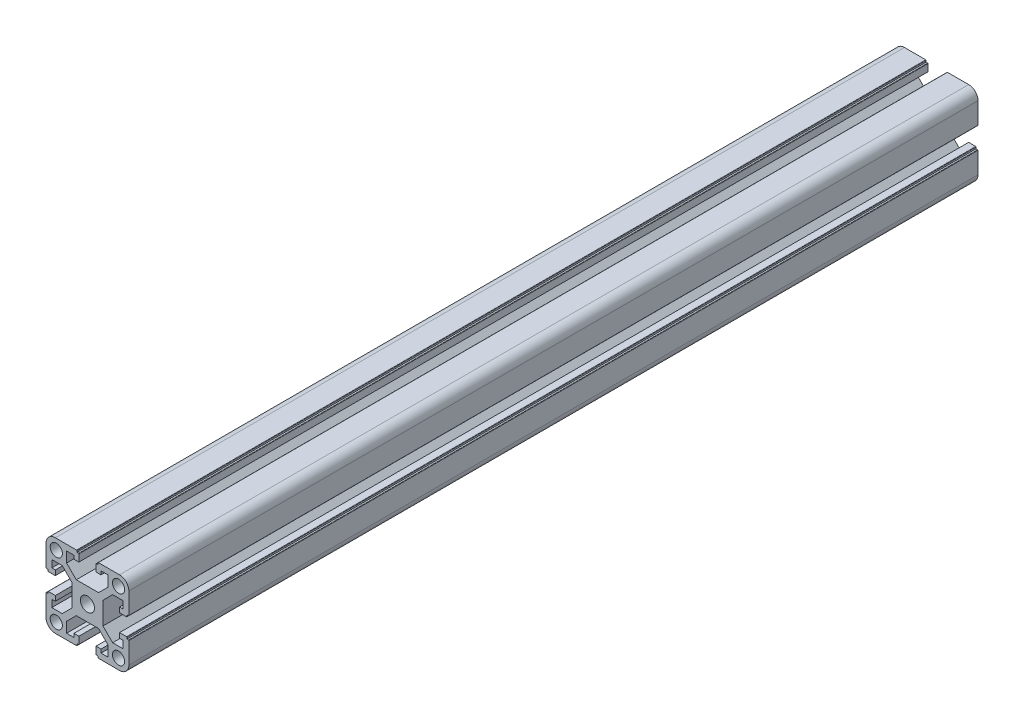
SolidWorks part; units mm, degrees
material "6061-T6 (SS)"
ref_plane "前视基准面" through (0, 0, 0) normal (0, 0, 1) x (1, 0, 0)
ref_plane "上视基准面" through (0, 0, 0) normal (0, 1, 0) x (1, 0, 0)
ref_plane "右视基准面" through (0, 0, 0) normal (1, 0, 0) x (0, 0, -1)
ref_plane "基准面1" through (0, 0, 50) normal (0, 0, 1) x (1, 0, 0)
sketch "草图1" plane through (0, 0, 50) normal (0, 0, 1) x (1, 0, 0)
  line L0 (-1518.245, 3588.0043) -> (-1518.245, 3582.9756)
  line L1 (-1518.245, 3582.9756) -> (-1522.9163, 3578.3043)
  line L2 (-1522.9163, 3578.3043) -> (-1533.6737, 3578.3043)
  line L3 (-1533.6737, 3578.3043) -> (-1538.345, 3582.9756)
  line L4 (-1538.345, 3582.9756) -> (-1538.345, 3588.0043)
  line L5 (-1538.345, 3588.0043) -> (-1534.845, 3588.0043)
  line L6 (-1534.845, 3588.0043) -> (-1534.845, 3586.3043)
  line L7 (-1534.845, 3586.3043) -> (-1532.445, 3586.3043)
  line L8 (-1532.445, 3586.3043) -> (-1532.445, 3589.7043)
  line L9 (-1532.645, 3589.9043) -> (-1533.345, 3589.9043)
  line L10 (-1533.345, 3589.9043) -> (-1533.345, 3590.6043)
  line L11 (-1533.545, 3590.8043) -> (-1543.795, 3590.8043)
  line L12 (-1548.295, 3586.3043) -> (-1548.295, 3576.0543)
  line L13 (-1548.095, 3575.8543) -> (-1547.395, 3575.8543)
  line L14 (-1547.395, 3575.8543) -> (-1547.395, 3575.1543)
  line L15 (-1547.195, 3574.9543) -> (-1543.795, 3574.9543)
  line L16 (-1543.795, 3574.9543) -> (-1543.795, 3577.3543)
  line L17 (-1543.795, 3577.3543) -> (-1545.495, 3577.3543)
  line L18 (-1545.495, 3577.3543) -> (-1545.495, 3580.8543)
  line L19 (-1545.495, 3580.8543) -> (-1540.4663, 3580.8543)
  line L20 (-1540.4663, 3580.8543) -> (-1535.795, 3576.183)
  line L21 (-1535.795, 3576.183) -> (-1535.795, 3565.4256)
  line L22 (-1535.795, 3565.4256) -> (-1540.4663, 3560.7543)
  line L23 (-1540.4663, 3560.7543) -> (-1545.495, 3560.7543)
  line L24 (-1545.495, 3560.7543) -> (-1545.495, 3564.2543)
  line L25 (-1545.495, 3564.2543) -> (-1543.795, 3564.2543)
  line L26 (-1543.795, 3564.2543) -> (-1543.795, 3566.6543)
  line L27 (-1543.795, 3566.6543) -> (-1547.195, 3566.6543)
  line L28 (-1547.395, 3566.4543) -> (-1547.395, 3565.7543)
  line L29 (-1547.395, 3565.7543) -> (-1548.095, 3565.7543)
  line L30 (-1548.295, 3565.5543) -> (-1548.295, 3555.3043)
  line L31 (-1543.795, 3550.8043) -> (-1533.545, 3550.8043)
  line L32 (-1533.345, 3551.0043) -> (-1533.345, 3551.7043)
  line L33 (-1533.345, 3551.7043) -> (-1532.645, 3551.7043)
  line L34 (-1532.445, 3551.9043) -> (-1532.445, 3555.3043)
  line L35 (-1532.445, 3555.3043) -> (-1534.845, 3555.3043)
  line L36 (-1534.845, 3555.3043) -> (-1534.845, 3553.6043)
  line L37 (-1534.845, 3553.6043) -> (-1538.345, 3553.6043)
  line L38 (-1538.345, 3553.6043) -> (-1538.345, 3558.633)
  line L39 (-1538.345, 3558.633) -> (-1533.6737, 3563.3043)
  line L40 (-1533.6737, 3563.3043) -> (-1522.9163, 3563.3043)
  line L41 (-1522.9163, 3563.3043) -> (-1518.245, 3558.633)
  line L42 (-1518.245, 3558.633) -> (-1518.245, 3553.6043)
  line L43 (-1518.245, 3553.6043) -> (-1521.745, 3553.6043)
  line L44 (-1521.745, 3553.6043) -> (-1521.745, 3555.3043)
  line L45 (-1521.745, 3555.3043) -> (-1524.145, 3555.3043)
  line L46 (-1524.145, 3555.3043) -> (-1524.145, 3551.9043)
  line L47 (-1523.945, 3551.7043) -> (-1523.245, 3551.7043)
  line L48 (-1523.245, 3551.7043) -> (-1523.245, 3551.0043)
  line L49 (-1523.045, 3550.8043) -> (-1512.795, 3550.8043)
  line L50 (-1508.295, 3555.3043) -> (-1508.295, 3565.5543)
  line L51 (-1508.495, 3565.7543) -> (-1509.195, 3565.7543)
  line L52 (-1509.195, 3565.7543) -> (-1509.195, 3566.4543)
  line L53 (-1509.395, 3566.6543) -> (-1512.795, 3566.6543)
  line L54 (-1512.795, 3566.6543) -> (-1512.795, 3564.2543)
  line L55 (-1512.795, 3564.2543) -> (-1511.095, 3564.2543)
  line L56 (-1511.095, 3564.2543) -> (-1511.095, 3560.7543)
  line L57 (-1511.095, 3560.7543) -> (-1516.1237, 3560.7543)
  line L58 (-1516.1237, 3560.7543) -> (-1520.795, 3565.4256)
  line L59 (-1520.795, 3565.4256) -> (-1520.795, 3576.183)
  line L60 (-1520.795, 3576.183) -> (-1516.1237, 3580.8543)
  line L61 (-1516.1237, 3580.8543) -> (-1511.095, 3580.8543)
  line L62 (-1511.095, 3580.8543) -> (-1511.095, 3577.3543)
  line L63 (-1511.095, 3577.3543) -> (-1512.795, 3577.3543)
  line L64 (-1512.795, 3577.3543) -> (-1512.795, 3574.9543)
  line L65 (-1512.795, 3574.9543) -> (-1509.395, 3574.9543)
  line L66 (-1509.195, 3575.1543) -> (-1509.195, 3575.8543)
  line L67 (-1509.195, 3575.8543) -> (-1508.495, 3575.8543)
  line L68 (-1508.295, 3576.0543) -> (-1508.295, 3586.3043)
  line L69 (-1512.795, 3590.8043) -> (-1523.045, 3590.8043)
  line L70 (-1523.245, 3590.6043) -> (-1523.245, 3589.9043)
  line L71 (-1523.245, 3589.9043) -> (-1523.945, 3589.9043)
  line L72 (-1524.145, 3589.7043) -> (-1524.145, 3586.3043)
  line L73 (-1524.145, 3586.3043) -> (-1521.745, 3586.3043)
  line L74 (-1521.745, 3586.3043) -> (-1521.745, 3588.0043)
  line L75 (-1521.745, 3588.0043) -> (-1518.245, 3588.0043)
  circle A0 centre (-1513.27, 3555.7793) radius 2.95
  circle A1 centre (-1528.295, 3570.8043) radius 3.4
  circle A2 centre (-1513.27, 3585.8293) radius 2.95
  arc A3 (-1532.445, 3589.7043) -> (-1532.645, 3589.9043) centre (-1532.645, 3589.7043) ccw
  arc A4 (-1533.345, 3590.6043) -> (-1533.545, 3590.8043) centre (-1533.545, 3590.6043) ccw
  arc A5 (-1543.795, 3590.8043) -> (-1548.295, 3586.3043) centre (-1543.795, 3586.3043) ccw
  arc A6 (-1548.295, 3576.0543) -> (-1548.095, 3575.8543) centre (-1548.095, 3576.0543) ccw
  arc A7 (-1547.395, 3575.1543) -> (-1547.195, 3574.9543) centre (-1547.195, 3575.1543) ccw
  arc A8 (-1547.195, 3566.6543) -> (-1547.395, 3566.4543) centre (-1547.195, 3566.4543) ccw
  arc A9 (-1548.095, 3565.7543) -> (-1548.295, 3565.5543) centre (-1548.095, 3565.5543) ccw
  arc A10 (-1548.295, 3555.3043) -> (-1543.795, 3550.8043) centre (-1543.795, 3555.3043) ccw
  arc A11 (-1533.545, 3550.8043) -> (-1533.345, 3551.0043) centre (-1533.545, 3551.0043) ccw
  arc A12 (-1532.645, 3551.7043) -> (-1532.445, 3551.9043) centre (-1532.645, 3551.9043) ccw
  arc A13 (-1524.145, 3551.9043) -> (-1523.945, 3551.7043) centre (-1523.945, 3551.9043) ccw
  arc A14 (-1523.245, 3551.0043) -> (-1523.045, 3550.8043) centre (-1523.045, 3551.0043) ccw
  arc A15 (-1512.795, 3550.8043) -> (-1508.295, 3555.3043) centre (-1512.795, 3555.3043) ccw
  arc A16 (-1508.295, 3565.5543) -> (-1508.495, 3565.7543) centre (-1508.495, 3565.5543) ccw
  arc A17 (-1509.195, 3566.4543) -> (-1509.395, 3566.6543) centre (-1509.395, 3566.4543) ccw
  arc A18 (-1509.395, 3574.9543) -> (-1509.195, 3575.1543) centre (-1509.395, 3575.1543) ccw
  arc A19 (-1508.495, 3575.8543) -> (-1508.295, 3576.0543) centre (-1508.495, 3576.0543) ccw
  arc A20 (-1508.295, 3586.3043) -> (-1512.795, 3590.8043) centre (-1512.795, 3586.3043) ccw
  arc A21 (-1523.045, 3590.8043) -> (-1523.245, 3590.6043) centre (-1523.045, 3590.6043) ccw
  arc A22 (-1523.945, 3589.9043) -> (-1524.145, 3589.7043) centre (-1523.945, 3589.7043) ccw
  circle A23 centre (-1543.32, 3585.8293) radius 2.95
  circle A24 centre (-1543.32, 3555.7793) radius 2.95
extrude "凸台-拉伸1" add sketch "草图1" against normal mid plane 410
ref_plane "基准面2" through (-1528.295, 0, 0) normal (1, 0, 0) x (0, 0, -1)
ref_plane "基准面3" through (0, 3570.8043, 0) normal (0, 1, 0) x (1, 0, 0)
